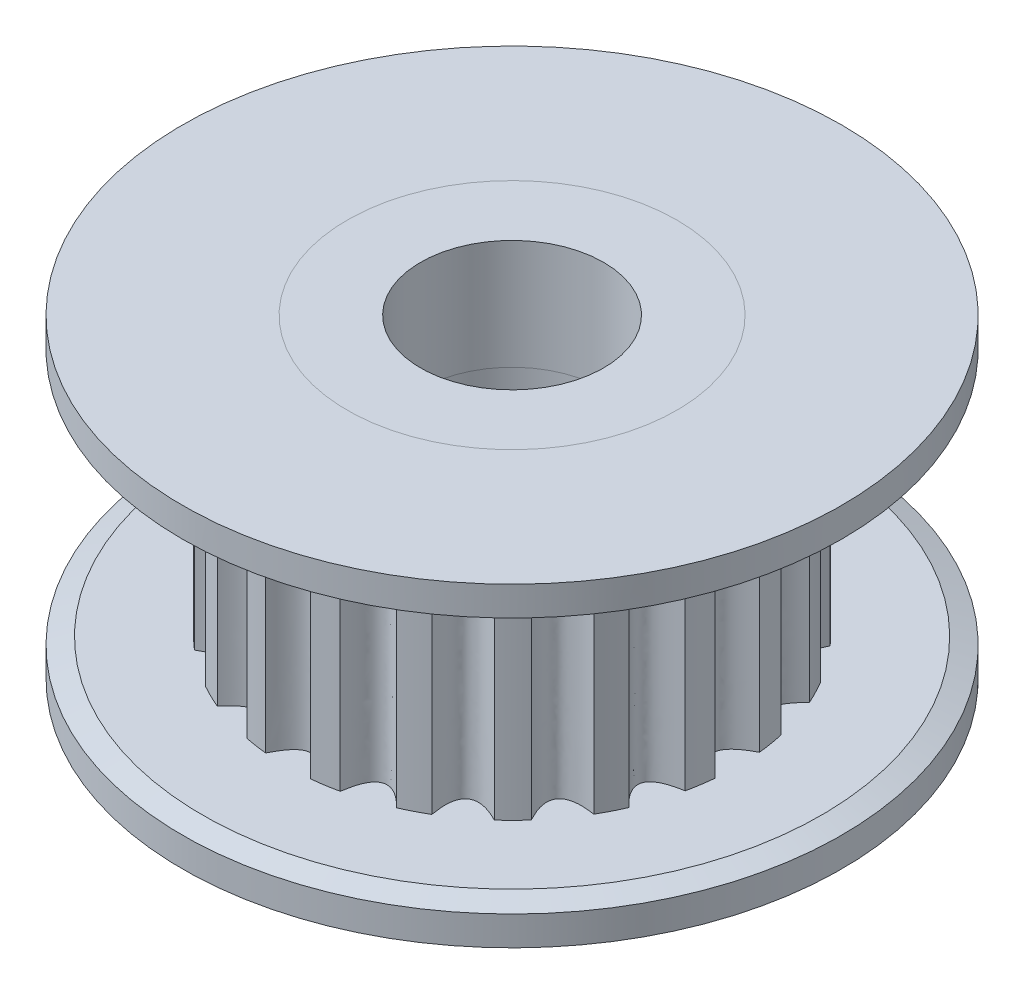
SolidWorks part; units mm, degrees
ref_plane "Plano frontal" through (0, 0, 0) normal (0, 0, 1) x (1, 0, 0)
ref_plane "Plano superior" through (0, 0, 0) normal (0, 1, 0) x (1, 0, 0)
ref_plane "Plano direito" through (0, 0, 0) normal (1, 0, 0) x (0, 0, -1)
sketch "Esboço1" plane through (0, 0, 0) normal (0, 0, 1) x (1, 0, 0)
  line L0 (-4.5, 0) -> (-9, 0)
  line L1 (-9, 0) -> (-9, 1)
  line L2 (-9, 1) -> (-6.15, 1)
  line L3 (-6.15, 1) -> (-6.15, 7.6)
  line L4 (-6.15, 7.6) -> (-9, 7.6)
  line L5 (-9, 7.6) -> (-9, 8.6)
  line L6 (-9, 8.6) -> (-4.5, 8.6)
  line L7 (-4.5, 0) -> (-4.5, 3)
  line L8 (-4.5, 3) -> (-2.5, 3)
  line L9 (-2.5, 3) -> (-2.5, 5.6)
  line L10 (-2.5, 5.6) -> (-4.5, 5.6)
  line L11 (-4.5, 5.6) -> (-4.5, 8.6)
  line L12 (0, 0) -> (0, 8.6) construction
  dimension "D1" = 1
  dimension "D2" = 9
  dimension "D3" = 6.6
  dimension "D4" = 6.15
  dimension "D5" = 4.5
  dimension "D6" = 2.5
  dimension "D7" = 3
revolve "Revolução1" add sketch "Esboço1" angle 360 about L12
chamfer "Chanfro1" distance 0.2 angle 70 1 edges at (0, 1, -9)
chamfer "Chanfro2" distance 0.2 angle 70 1 edges at (0, 7.6, -9)
sketch "Esboço2" plane through (0, 0, 0) normal (0, 0, 1) x (1, 0, 0)
  line L0 (-2.5, 0) -> (-2.5, 3)
  line L1 (-9, 0) -> (9, 0) construction
  line L2 (-2.5, 3) -> (-4.5, 3)
  line L3 (-4.5, 3) -> (-4.5, 0)
  line L4 (-4.5, 0) -> (-2.5, 0)
  line L5 (9, 8.6) -> (-9, 8.6) construction
  line L6 (-4.5, 5.6) -> (-2.5, 5.6)
  line L7 (-4.5, 5.6) -> (-4.5, 8.6)
  line L8 (-4.5, 8.6) -> (-2.5, 8.6)
  line L9 (-2.5, 5.6) -> (-2.5, 8.6)
  line L10 (0, 0) -> (0, 8.6) construction
  dimension "D1" = 2.5
  dimension "D2" = 4.5
  dimension "D3" = 3
revolve "Revolução2" add sketch "Esboço2" angle 360 about L10
sketch "Esboço3" plane through (0, 7.6, 0) normal (0, -1, 0) x (1, 0, 0)
  line L0 (0, 6.15) -> (0, 5.5) construction
  circle A0 centre (0, 0) radius 6.15 construction
  arc A1 (0.6113, 6.1195) -> (-0.6113, 6.1195) centre (0, 0) ccw
  arc A2 (2.4776, 5.6289) -> (1.3152, 6.0077) centre (0, 0) ccw
  arc A3 (4.0999, 4.584) -> (3.1122, 5.3044) centre (0, 0) ccw
  arc A4 (5.3186, 3.0878) -> (4.6028, 4.0788) centre (0, 0) ccw
  arc A5 (6.0137, 1.2876) -> (5.6402, 2.4517) centre (0, 0) ccw
  arc A6 (6.1167, -0.6394) -> (6.1223, 0.5832) centre (0, 0) ccw
  arc A7 (5.6174, -2.5034) -> (6.0016, -1.3428) centre (0, 0) ccw
  arc A8 (4.5651, -4.1209) -> (5.2901, -3.1365) centre (0, 0) ccw
  arc A9 (3.0634, -5.3328) -> (4.0577, -4.6215) centre (0, 0) ccw
  arc A10 (1.26, -6.0195) -> (2.4258, -5.6514) centre (0, 0) ccw
  arc A11 (-0.6674, -6.1137) -> (0.5551, -6.1249) centre (0, 0) ccw
  arc A12 (-2.5291, -5.6059) -> (-1.3703, -5.9954) centre (0, 0) ccw
  arc A13 (-4.1418, -4.5462) -> (-3.1608, -5.2756) centre (0, 0) ccw
  arc A14 (-5.3468, -3.0389) -> (-4.64, -4.0364) centre (0, 0) ccw
  arc A15 (-6.0253, -1.2324) -> (-5.6625, -2.3998) centre (0, 0) ccw
  arc A16 (-6.1105, 0.6955) -> (-6.1274, -0.5269) centre (0, 0) ccw
  arc A17 (-5.5942, 2.5548) -> (-5.989, 1.3978) centre (0, 0) ccw
  arc A18 (-4.5271, 4.1627) -> (-5.261, 3.185) centre (0, 0) ccw
  arc A19 (-3.0143, 5.3607) -> (-4.0151, 4.6585) centre (0, 0) ccw
  arc A20 (-1.2047, 6.0309) -> (-2.3738, 5.6734) centre (0, 0) ccw
  spline S0 degree 2 poles (0.6113, 6.1195) (0, 4.8805) (-0.6113, 6.1195) knots 0 0 0 1 1 1
  spline S1 degree 2 poles (2.4776, 5.6289) (1.5075, 4.6418) (1.3152, 6.0077) knots 0 0 0 1 1 1
  spline S2 degree 2 poles (4.0999, 4.584) (2.8676, 3.949) (3.1122, 5.3044) knots 0 0 0 1 1 1
  spline S3 degree 2 poles (5.3186, 3.0878) (3.9471, 2.8701) (4.6028, 4.0788) knots 0 0 0 1 1 1
  spline S4 degree 2 poles (6.0137, 1.2876) (4.6405, 1.5105) (5.6402, 2.4517) knots 0 0 0 1 1 1
  spline S5 degree 2 poles (6.1167, -0.6394) (4.8799, 0.0032) (6.1223, 0.5832) knots 0 0 0 1 1 1
  spline S6 degree 2 poles (5.6174, -2.5034) (4.642, -1.5042) (6.0016, -1.3428) knots 0 0 0 1 1 1
  spline S7 degree 2 poles (4.5651, -4.1209) (3.9501, -2.8643) (5.2901, -3.1365) knots 0 0 0 1 1 1
  spline S8 degree 2 poles (3.0634, -5.3328) (2.872, -3.9441) (4.0577, -4.6215) knots 0 0 0 1 1 1
  spline S9 degree 2 poles (1.26, -6.0195) (1.5132, -4.638) (2.4258, -5.6514) knots 0 0 0 1 1 1
  spline S10 degree 2 poles (-0.6674, -6.1137) (0.0066, -4.8782) (0.5551, -6.1249) knots 0 0 0 1 1 1
  spline S11 degree 2 poles (-2.5291, -5.6059) (-1.5004, -4.6412) (-1.3703, -5.9954) knots 0 0 0 1 1 1
  spline S12 degree 2 poles (-4.1418, -4.5462) (-2.8603, -3.9505) (-3.1608, -5.2756) knots 0 0 0 1 1 1
  spline S13 degree 2 poles (-5.3468, -3.0389) (-3.9402, -2.8735) (-4.64, -4.0364) knots 0 0 0 1 1 1
  spline S14 degree 2 poles (-6.0253, -1.2324) (-4.6345, -1.5158) (-5.6625, -2.3998) knots 0 0 0 1 1 1
  spline S15 degree 2 poles (-6.1105, 0.6955) (-4.8754, -0.0103) (-6.1274, -0.5269) knots 0 0 0 1 1 1
  spline S16 degree 2 poles (-5.5942, 2.5548) (-4.6395, 1.4959) (-5.989, 1.3978) knots 0 0 0 1 1 1
  spline S17 degree 2 poles (-4.5271, 4.1627) (-3.9501, 2.8553) (-5.261, 3.185) knots 0 0 0 1 1 1
  spline S18 degree 2 poles (-3.0143, 5.3607) (-2.8747, 3.9351) (-4.0151, 4.6585) knots 0 0 0 1 1 1
  spline S19 degree 2 poles (-1.2047, 6.0309) (-1.5185, 4.6297) (-2.3738, 5.6734) knots 0 0 0 1 1 1
  point P67 (0, 0)
  dimension "D1" = 0.65
  dimension "D3" = 0.6
  dimension "D2" = 20
extrude "Corte-extrusão1" cut sketch "Esboço3" along normal up to surface (6.6 mm away) up to face at (0, 1, -8.4505)
